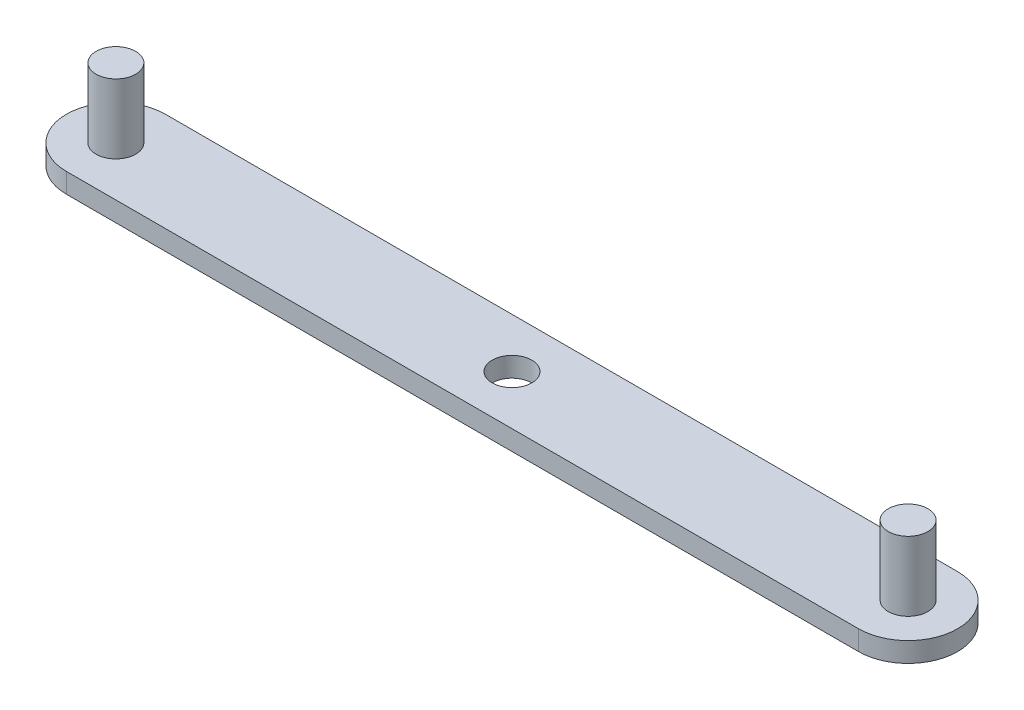
SolidWorks part; units mm, degrees
ref_plane "前视基准面" through (0, 0, 0) normal (0, 0, 1) x (1, 0, 0)
ref_plane "上视基准面" through (0, 0, 0) normal (0, 1, 0) x (1, 0, 0)
ref_plane "右视基准面" through (0, 0, 0) normal (1, 0, 0) x (0, 0, -1)
sketch "草图1" plane through (0, 0, 0) normal (0, 1, 0) x (1, 0, 0)
  line L1 (-65, 5) -> (15, 5)
  line L3 (-65, -5) -> (15, -5)
  arc A0 (-65, 5) -> (-65, -5) centre (-65, 0) ccw
  arc A1 (15, -5) -> (15, 5) centre (15, 0) ccw
  point P0 (0, 0)
  dimension "D1" = 80
extrude "凸台-拉伸1" add sketch "草图1" along normal blind 2
sketch "草图2" plane through (0, 2, 0) normal (0, 1, 0) x (1, 0, 0)
  line L0 (-65, 5) -> (-65, -5)
  circle A1 centre (-65, 0) radius 2
  circle A2 centre (15, 0) radius 2
extrude "凸台-拉伸2" add sketch "草图2" along normal blind 7 contours A2 | L0 A1 | L0 A1
sketch "草图4" plane through (0, 0, 0) normal (0, -1, 0) x (1, 0, 0)
  line L0 (-65, -5) -> (15, 5)
  circle A0 centre (-25, 0) radius 2
extrude "切除-拉伸2" cut sketch "草图4" against normal blind 10 contours L0 A0 | L0 A0
